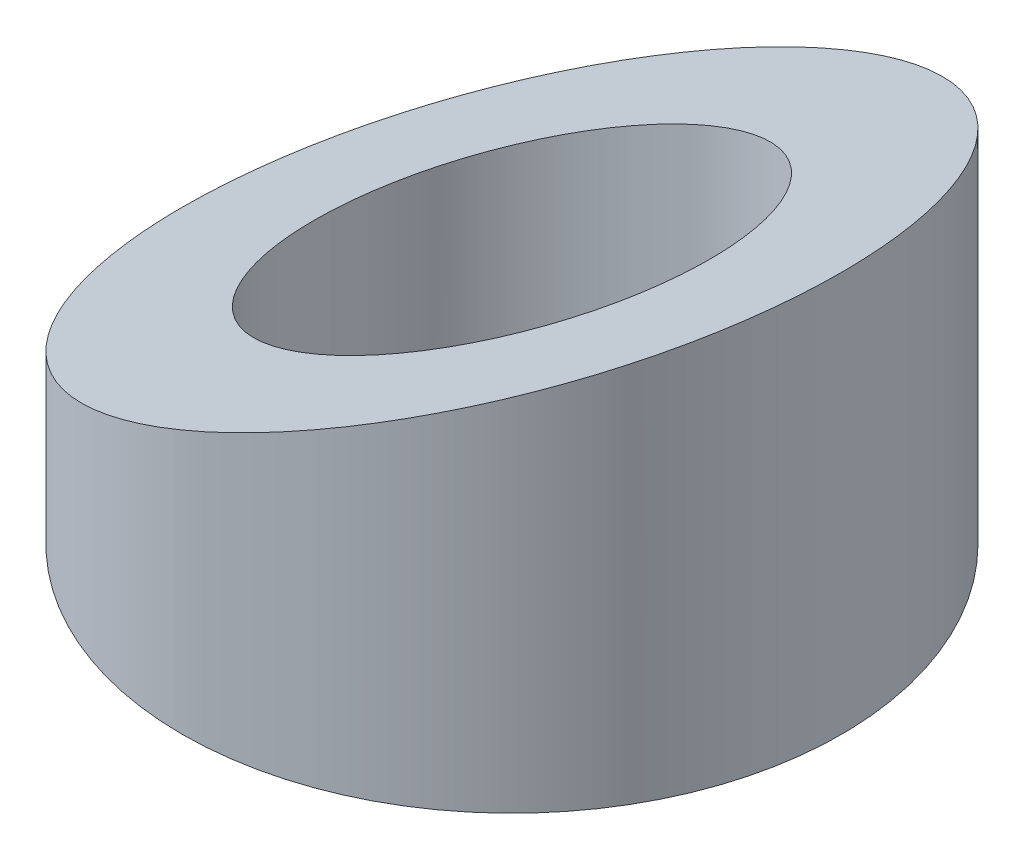
SolidWorks part; units mm, degrees
ref_plane "前视基准面" through (0, 0, 0) normal (0, 0, 1) x (1, 0, 0)
ref_plane "上视基准面" through (0, 0, 0) normal (0, 1, 0) x (1, 0, 0)
ref_plane "右视基准面" through (0, 0, 0) normal (1, 0, 0) x (0, 0, -1)
sketch "草图1" plane through (0, 0, 0) normal (0, 1, 0) x (1, 0, 0)
  circle A0 centre (0, 0) radius 15
  dimension "D1" = 30
extrude "凸台-拉伸1" add sketch "草图1" along normal blind 20
sketch "草图2" plane through (0, 0, 0) normal (0, 0, 1) x (1, 0, 0)
  line L0 (-15, 5.7868) -> (15, 18.2132)
  line L1 (15, 18.2132) -> (15, 34.074)
  line L2 (15, 34.074) -> (-15, 34.074)
  line L3 (-15, 34.074) -> (-15, 5.7868)
  line L4 (0, 34.074) -> (0, 12) construction
  line L5 (-15, 0) -> (15, 0) construction
  dimension "D1" = 30
  dimension "D2" = 0
  dimension "D3" = 12
  dimension "D4" = 22.5
extrude "切除-拉伸1" cut sketch "草图2" against normal mid plane 33
ref_point "点1"
sketch "草图3" plane through (0, 0, 0) normal (0, 0, 1) x (1, 0, 0)
  line L0 (-15, 0) -> (15, 0) construction
  line L1 (15, 0) -> (15, 18.2132) construction
  line L2 (15, 18.2132) -> (-15, 5.7868) construction
  line L3 (-15, 5.7868) -> (-15, 0) construction
sketch "草图5" plane through (-4.2426, 10.2426, 0) normal (-0.3827, 0.9239, 0) x (0.9239, 0.3827, 0)
  line L0 (4.5922, -15) -> (4.5922, 15) construction
sketch "草图6" plane through (0, 0, 0) normal (1, 0, 0) x (0, 0, -1)
  line L0 (-15, 12) -> (-15, 0) construction
  line L1 (-15, 0) -> (15, 0) construction
  line L2 (15, 0) -> (15, 12) construction
  line L3 (0, 12) -> (0, 0)
sketch "草图7" plane through (0, 0, 0) normal (0, -1, 0) x (1, 0, 0)
  circle A0 centre (0, 0) radius 9
  dimension "D1" = 18
extrude "切除-拉伸2" cut sketch "草图7" against normal blind 24.5
sketch "草图8" plane through (-4.2426, 10.2426, 0) normal (-0.3827, 0.9239, 0) x (0.9239, 0.3827, 0)
  circle A0 centre (4.5922, 0) radius 4.0948
